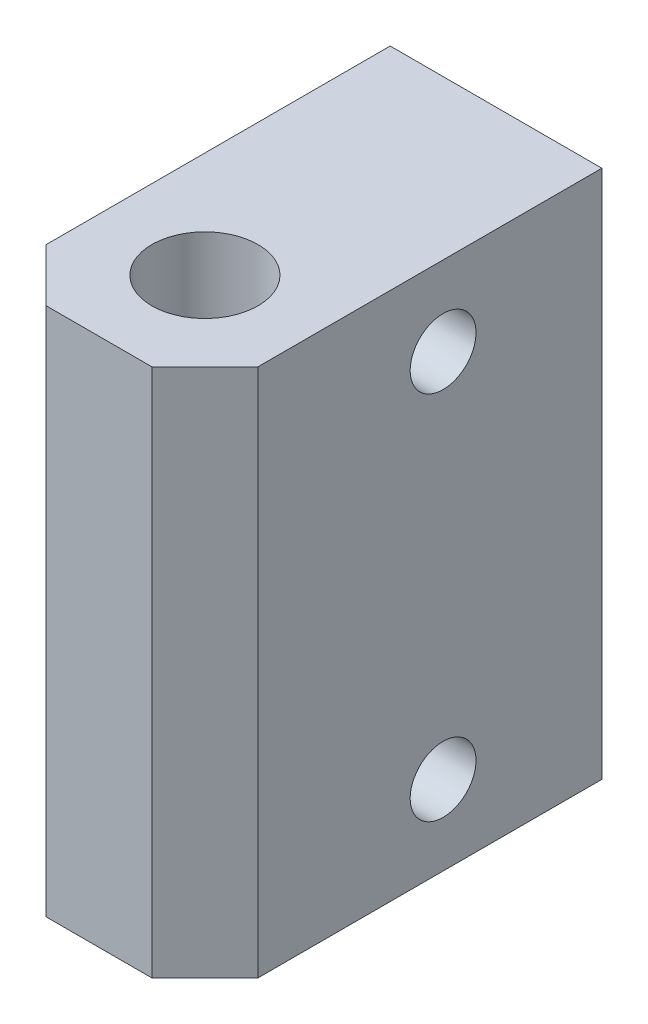
SolidWorks part; units mm, degrees
material "6061-T6 (SS)"
ref_plane "Front Plane" through (0, 0, 0) normal (0, 0, 1) x (1, 0, 0)
ref_plane "Top Plane" through (0, 0, 0) normal (0, 1, 0) x (1, 0, 0)
ref_plane "Right Plane" through (0, 0, 0) normal (1, 0, 0) x (0, 0, -1)
sketch "Sketch1" plane through (0, 0, 0) normal (0, 1, 0) x (1, 0, 0)
  line L0 (0, 0) -> (0, -8.6954) construction
  line L1 (-8, -8) -> (8, -8)
  line L2 (-8, -8) -> (-8, 22)
  line L3 (-8, 22) -> (8, 22)
  line L4 (8, -8) -> (8, 22)
  line L5 (-8, -8) -> (8, 22) construction
  line L6 (-8, 22) -> (8, -8) construction
  line L8 (-14.6536, 14.2544) -> (14.6536, 14.2544) construction
  line L9 (-14.6536, 14.2544) -> (-14.6536, 6.3296) construction
  line L10 (-14.6536, 6.3296) -> (14.6536, 6.3296) construction
  line L11 (14.6536, 14.2544) -> (14.6536, 6.3296) construction
  line L12 (-14.6536, 14.2544) -> (14.6536, 6.3296) construction
  line L13 (-14.6536, 6.3296) -> (14.6536, 14.2544) construction
  circle A0 centre (0, 0) radius 3.9751 construction
  point P3 (0, 7)
  point P8 (0, 10.292)
  dimension "D1" = 7.9502
  dimension "D2" = 16
  dimension "D3" = 8
  dimension "D4" = 7.9248
  dimension "D5" = 30
extrude "Boss-Extrude1" add sketch "Sketch1" along normal blind 40
hole_wizard "O (0.316) Diameter Hole1" positions "Sketch3" profile "Sketch2" hole size "O" standard "ANSI Inch"
sketch "Sketch3" plane through (0, 40, 0) normal (0, 1, 0) x (1, 0, 0)
  point P0 (0, 0)
sketch "Sketch2" plane through (0, 40, 0) normal (1, 0, 0) x (0, 0, 1)
  line L0 (0, 0) -> (0, 17.4114)
  line L1 (0, 17.4114) -> (4.0132, 15)
  line L2 (4.0132, 15) -> (4.0132, 0)
  line L5 (4.0132, 0) -> (0, 0)
  line L10 (0, 17.4114) -> (-4.0132, 15) construction
  line L11 (0, -6.35) -> (0, 107.95) construction
  dimension "Hole Dia." = 8.0264
  dimension "Hole Depth" = 15
  dimension "Drill Angle" = 118
hole_wizard "#10 Clearance Hole1" positions "Sketch5" profile "Sketch4" hole size "#10" standard "ANSI Inch" end condition through all
sketch "Sketch5" plane through (-8, 0, 0) normal (-1, 0, 0) x (0, 0, 1)
  line L0 (0, 0) -> (0, 5.0375) construction
  line L2 (-10, 6) -> (-10, 34) construction
  line L3 (8, 20) -> (10.2723, 20) construction
  line L4 (8, 40) -> (8, 0) construction
  point P0 (-10, 34)
  point P2 (-10, 6)
  point P16 (-10, 20)
  dimension "D1" = 28
  dimension "D2" = 10
sketch "Sketch4" plane through (-8, 34, -10) normal (0, 1, 0) x (0, 0, 1)
  line L0 (0, 0) -> (0, 16)
  line L1 (0, 16) -> (2.4892, 16)
  line L2 (2.4892, 16) -> (2.4892, 0)
  line L5 (2.4892, 0) -> (0, 0)
  line L11 (0, -6.35) -> (0, 107.95) construction
  dimension "Thru Hole Dia." = 4.9784
  dimension "Thru Hole Depth" = 16
chamfer "Chamfer1" distance 4 angle 45 2 edges at (8, 20, 8) (-8, 20, 8)
